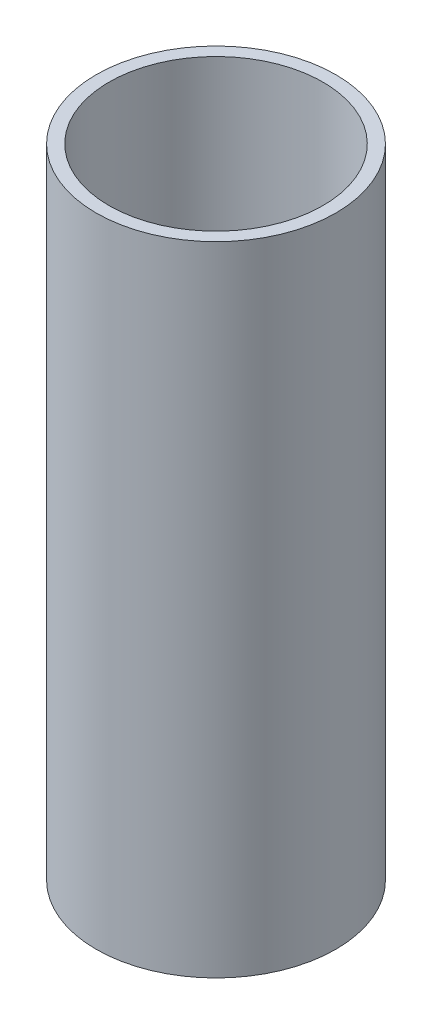
SolidWorks part; units mm, degrees
ref_plane "Front Plane" through (0, 0, 0) normal (0, 0, 1) x (1, 0, 0)
ref_plane "Top Plane" through (0, 0, 0) normal (0, 1, 0) x (1, 0, 0)
ref_plane "Right Plane" through (0, 0, 0) normal (1, 0, 0) x (0, 0, -1)
sketch "Sketch1" plane through (0, 0, 0) normal (0, 1, 0) x (1, 0, 0)
  circle A0 centre (0, 0) radius 14
  circle A1 centre (0, 0) radius 12.5
extrude "Boss-Extrude1" add sketch "Sketch1" along normal blind 74.498
scale "Scale1" scale about centroid uniform scaling yes scale factor 0.75
